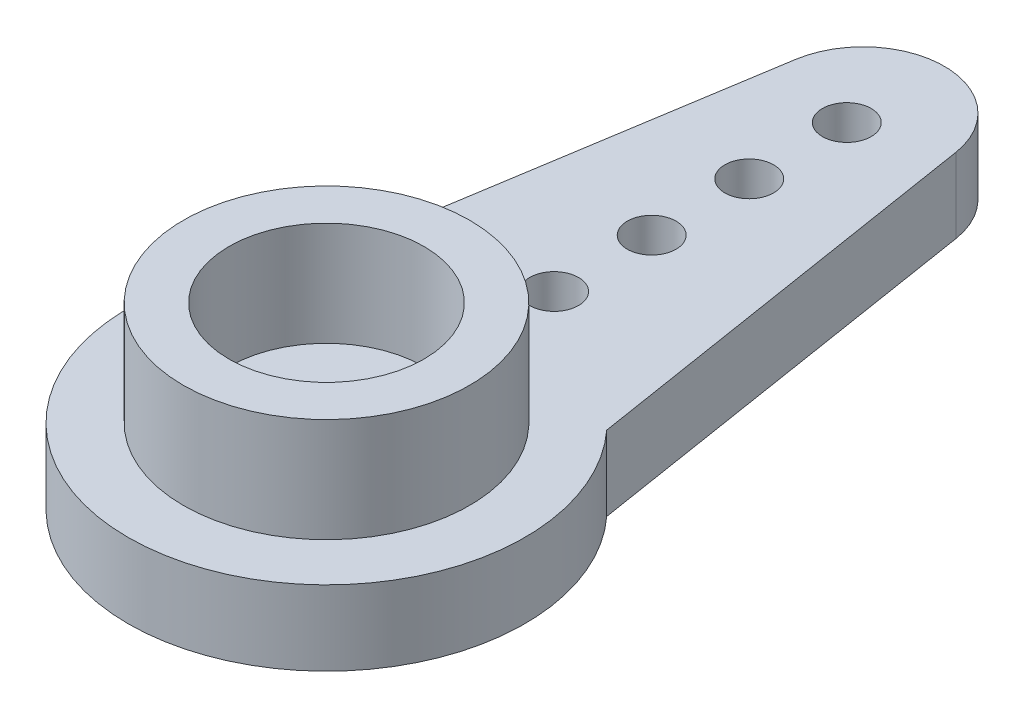
SolidWorks part; units mm, degrees
ref_plane "前视基准面" through (0, 0, 0) normal (0, 0, 1) x (1, 0, 0)
ref_plane "上视基准面" through (0, 0, 0) normal (0, 1, 0) x (1, 0, 0)
ref_plane "右视基准面" through (0, 0, 0) normal (1, 0, 0) x (0, 0, -1)
sketch "Sketch1" plane through (0, 0, 0) normal (0, 1, 0) x (1, 0, 0)
  circle A0 centre (0, 0) radius 6.1
  circle A1 centre (0, 0) radius 1.5
  dimension "D1" = 12.2
  dimension "D2" = 3
extrude "Boss-Extrude1" add sketch "Sketch1" along normal blind 2.3
sketch "Sketch2" plane through (0, 2.3, 0) normal (0, 1, 0) x (1, 0, 0)
  circle A0 centre (0, 0) radius 4.4
  circle A1 centre (0, 0) radius 3
  dimension "D1" = 8.8
  dimension "D2" = 6
extrude "Boss-Extrude2" add sketch "Sketch2" along normal blind 3.2
sketch "Sketch3" plane through (0, 0, 0) normal (0, -1, 0) x (1, 0, 0)
  line L0 (0, 0) -> (0, -19) construction
  line L1 (-2.469, -16.8925) -> (-4.5, -4.1183)
  line L2 (2.469, -16.8925) -> (4.5, -4.1183)
  arc A0 (-2.469, -16.8925) -> (2.469, -16.8925) centre (0, -16.5) ccw
  circle A1 centre (0, 0) radius 6.1 construction
  circle A2 centre (0, 0) radius 6.1
  circle A3 centre (0, -7) radius 0.75
  circle A4 centre (0, -10) radius 0.75
  circle A5 centre (0, -13) radius 0.75
  circle A6 centre (0, -16) radius 0.75
  circle A7 centre (0, 0) radius 1.5 construction
  point P12 (-6.1, 0)
  circle M3 centre (0, 0) radius 6.1
  dimension "D2" = 2.5
  dimension "D4" = 1.5
  dimension "D5" = 3
  dimension "D6" = 3
  dimension "D7" = 3
  dimension "D8" = 7
  dimension "D1" = 19
  dimension "D3" = 1.6
extrude "Boss-Extrude3" add sketch "Sketch3" against normal blind 2.3 contours A2 L0 A3 A4 A5 A6 A0 L2 | L0 L1 A0 A6 A5 A4 A3 M3
